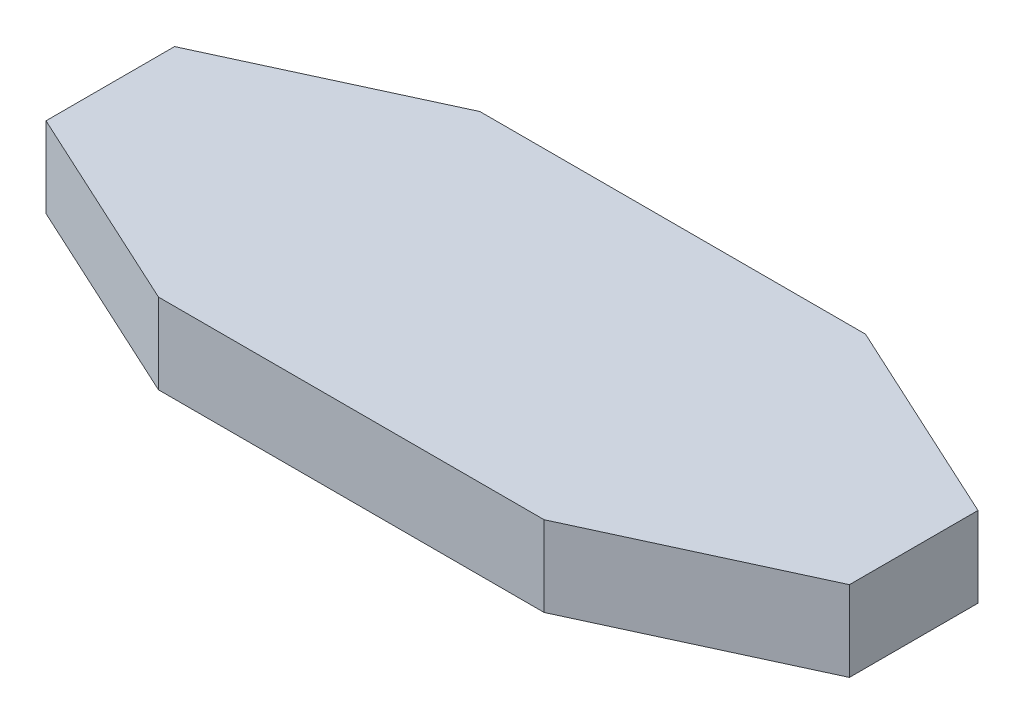
SolidWorks part; units mm, degrees
ref_plane "Front Plane" through (0, 0, 0) normal (0, 0, 1) x (1, 0, 0)
ref_plane "Top Plane" through (0, 0, 0) normal (0, 1, 0) x (1, 0, 0)
ref_plane "Right Plane" through (0, 0, 0) normal (1, 0, 0) x (0, 0, -1)
sketch "Sketch1" plane through (0, 0, 0) normal (0, 1, 0) x (1, 0, 0)
  line L0 (0, 50) -> (0, -50) construction
  line L1 (-125, 0) -> (125, 0) construction
  line L2 (-60, 50) -> (60, 50)
  line L5 (60, -50) -> (-60, -50)
  line L8 (125, 20) -> (125, -20)
  line L9 (125, -20) -> (60, -50)
  line L10 (60, 50) -> (125, 20)
  line L11 (-125, -20) -> (-60, -50)
  line L12 (-125, 20) -> (-125, -20)
  line L13 (-60, 50) -> (-125, 20)
  point P4 (0, 0)
  point P8 (0, 0)
  point P11 (0, 50)
  point P16 (125, 0)
extrude "Boss-Extrude1" add sketch "Sketch1" along normal blind 25 contours L13 L12 L11 L5 L9 L8 L10 L2
sketch "Sketch3" plane through (0, 25, 0) normal (0, 1, 0) x (1, 0, 0)
  line L0 (0, 0) -> (0, -35) construction
  line L5 (-125, -20) -> (-60, -50) construction
  line L6 (-60, 50) -> (-125, 20) construction
  line L7 (-92.5, 35) -> (92.5, 35) construction
  line L8 (60, 50) -> (125, 20) construction
  line L10 (125, -20) -> (60, -50) construction
  line L11 (92.5, -35) -> (-92.5, -35) construction
  line L12 (-92.5, -35) -> (0, 0) construction
  line L13 (0, 0) -> (92.5, -35) construction
  line L14 (92.5, 35) -> (0, 0) construction
  line L15 (-92.5, 35) -> (0, 0) construction
  line L16 (0, 0) -> (0, 35) construction
  circle A6 centre (0, -35) radius 7
  circle A7 centre (78.4707, -29.6916) radius 7
  circle A8 centre (0, 35) radius 7
  circle A10 centre (-78.4707, -29.6916) radius 7
  circle A11 centre (-78.4707, 29.6916) radius 7
  circle A12 centre (78.4707, 29.6916) radius 7
  dimension "D1" = 15
  dimension "D2" = 15
  dimension "D3" = 15
